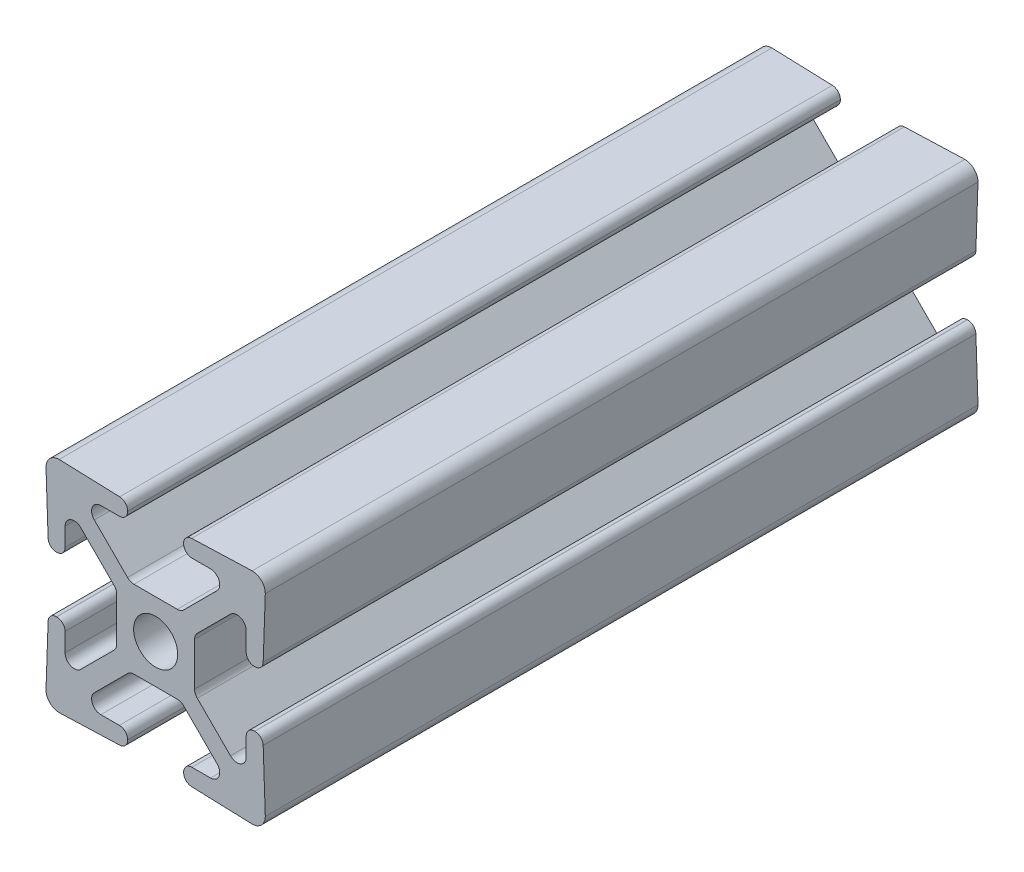
SolidWorks part; units mm, degrees
material "6061 Alloy"
ref_plane "Front Plane" through (0, 0, 0) normal (0, 0, 1) x (1, 0, 0)
ref_plane "Top Plane" through (0, 0, 0) normal (0, 1, 0) x (1, 0, 0)
ref_plane "Right Plane" through (0, 0, 0) normal (1, 0, 0) x (0, 0, -1)
sketch "Sketch1" plane through (0, 0, 0) normal (0, 0, 1) x (1, 0, 0)
  line L1 (3.2385, -11.4554) -> (3.2385, -11.4907)
  line L2 (-7.1065, 8.6691) -> (-3.2584, 4.821)
  line L3 (-3.2385, 11.4907) -> (-3.2385, 11.4554)
  line L6 (-4.2037, 10.4902) -> (-6.3521, 10.4902)
  line L7 (-11.176, 12.7) -> (-4.17, 12.4553)
  line L8 (11.4554, 3.2385) -> (11.4907, 3.2385)
  line L9 (11.4554, -3.2385) -> (11.4907, -3.2385)
  line L11 (-4.821, 3.2584) -> (-8.6691, 7.1065)
  line L12 (-10.4902, 6.3521) -> (-10.4902, 4.2037)
  line L13 (-12.7, 11.176) -> (-12.4553, 4.17)
  line L15 (-4.5085, -2.504) -> (-4.5085, 2.504)
  line L16 (6.3521, -10.4902) -> (4.2037, -10.4902)
  line L22 (-2.504, 4.5085) -> (2.504, 4.5085)
  line L23 (-3.2584, -4.821) -> (-7.1065, -8.6691)
  line L24 (-11.176, -12.7) -> (-4.17, -12.4553)
  line L25 (-12.7, -11.176) -> (-12.4553, -4.17)
  line L26 (-10.4902, -4.2037) -> (-10.4902, -6.3521)
  line L27 (-8.6691, -7.1065) -> (-4.821, -3.2584)
  line L36 (8.6691, -7.1065) -> (4.821, -3.2584)
  line L38 (10.4902, -4.2037) -> (10.4902, -6.3521)
  line L39 (12.7, -11.176) -> (12.4553, -4.17)
  line L42 (11.176, -12.7) -> (4.17, -12.4553)
  line L43 (3.2584, -4.821) -> (7.1065, -8.6691)
  line L47 (4.5085, -2.504) -> (4.5085, 2.504)
  line L48 (12.7, 11.176) -> (12.4553, 4.17)
  line L49 (10.4902, 6.3521) -> (10.4902, 4.2037)
  line L50 (4.821, 3.2584) -> (8.6691, 7.1065)
  line L52 (2.504, -4.5085) -> (-2.504, -4.5085)
  line L56 (11.176, 12.7) -> (4.17, 12.4553)
  line L57 (4.2037, 10.4902) -> (6.3521, 10.4902)
  line L59 (-6.3521, -10.4902) -> (-4.2037, -10.4902)
  line L60 (3.2385, 11.4907) -> (3.2385, 11.4554)
  line L61 (7.1065, 8.6691) -> (3.2584, 4.821)
  line L66 (-11.4554, -3.2385) -> (-11.4907, -3.2385)
  line L68 (-11.4554, 3.2385) -> (-11.4907, 3.2385)
  line L74 (-3.2385, -11.4554) -> (-3.2385, -11.4907)
  arc A1 (-3.2385, 11.4907) -> (-4.17, 12.4553) centre (-4.2037, 11.4907) ccw
  arc A4 (-4.2037, 10.4902) -> (-3.2385, 11.4554) centre (-4.2037, 11.4554) ccw
  arc A6 (-6.3521, 10.4902) -> (-7.1065, 8.6691) centre (-6.3521, 9.4234) ccw
  arc A8 (-12.4553, 4.17) -> (-11.4907, 3.2385) centre (-11.4907, 4.2037) ccw
  arc A9 (-11.176, 12.7) -> (-12.7, 11.176) centre (-11.176, 11.176) ccw
  arc A12 (-8.6691, 7.1065) -> (-10.4902, 6.3521) centre (-9.4234, 6.3521) ccw
  arc A13 (-11.4554, 3.2385) -> (-10.4902, 4.2037) centre (-11.4554, 4.2037) ccw
  arc A16 (-4.821, -3.2584) -> (-4.5085, -2.504) centre (-5.5753, -2.504) ccw
  arc A17 (-4.5085, 2.504) -> (-4.821, 3.2584) centre (-5.5753, 2.504) ccw
  arc A22 (3.2584, 4.821) -> (2.504, 4.5085) centre (2.504, 5.5753) cw
  arc A23 (10.4902, -6.3521) -> (8.6691, -7.1065) centre (9.4234, -6.3521) cw
  arc A24 (10.4902, -4.2037) -> (11.4554, -3.2385) centre (11.4554, -4.2037) cw
  arc A25 (11.4907, -3.2385) -> (12.4553, -4.17) centre (11.4907, -4.2037) cw
  arc A26 (12.7, -11.176) -> (11.176, -12.7) centre (11.176, -11.176) cw
  arc A28 (-2.504, -4.5085) -> (-3.2584, -4.821) centre (-2.504, -5.5753) ccw
  arc A29 (-4.17, -12.4553) -> (-3.2385, -11.4907) centre (-4.2037, -11.4907) ccw
  arc A30 (-3.2385, -11.4554) -> (-4.2037, -10.4902) centre (-4.2037, -11.4554) ccw
  arc A31 (-7.1065, -8.6691) -> (-6.3521, -10.4902) centre (-6.3521, -9.4234) ccw
  arc A32 (-12.7, -11.176) -> (-11.176, -12.7) centre (-11.176, -11.176) ccw
  arc A33 (-11.4907, -3.2385) -> (-12.4553, -4.17) centre (-11.4907, -4.2037) ccw
  arc A34 (-10.4902, -4.2037) -> (-11.4554, -3.2385) centre (-11.4554, -4.2037) ccw
  arc A35 (-10.4902, -6.3521) -> (-8.6691, -7.1065) centre (-9.4234, -6.3521) ccw
  arc A36 (7.1065, -8.6691) -> (6.3521, -10.4902) centre (6.3521, -9.4234) cw
  arc A37 (3.2385, -11.4554) -> (4.2037, -10.4902) centre (4.2037, -11.4554) cw
  arc A38 (-3.2584, 4.821) -> (-2.504, 4.5085) centre (-2.504, 5.5753) ccw
  arc A39 (4.17, -12.4553) -> (3.2385, -11.4907) centre (4.2037, -11.4907) cw
  arc A40 (2.504, -4.5085) -> (3.2584, -4.821) centre (2.504, -5.5753) cw
  circle A44 centre (0, 0) radius 2.5527
  arc A45 (4.5085, 2.504) -> (4.821, 3.2584) centre (5.5753, 2.504) cw
  arc A46 (4.821, -3.2584) -> (4.5085, -2.504) centre (5.5753, -2.504) cw
  arc A47 (11.4554, 3.2385) -> (10.4902, 4.2037) centre (11.4554, 4.2037) cw
  arc A48 (8.6691, 7.1065) -> (10.4902, 6.3521) centre (9.4234, 6.3521) cw
  arc A49 (11.176, 12.7) -> (12.7, 11.176) centre (11.176, 11.176) cw
  arc A53 (12.4553, 4.17) -> (11.4907, 3.2385) centre (11.4907, 4.2037) cw
  arc A54 (6.3521, 10.4902) -> (7.1065, 8.6691) centre (6.3521, 9.4234) cw
  arc A56 (4.2037, 10.4902) -> (3.2385, 11.4554) centre (4.2037, 11.4554) cw
  arc A58 (3.2385, 11.4907) -> (4.17, 12.4553) centre (4.2037, 11.4907) cw
  dimension "D5" = 5.1054
  dimension "D1" = 12.7
  dimension "D2" = 25.4
  dimension "D3" = 25.4
  dimension "D4" = 12.7
extrude "Extrude1" add sketch "Sketch1" along normal blind 82.55
sketch "Sketch2" plane through (0, 0, 0) normal (0, 0, -1) x (-1, 0, 0)
  point P0 (0, 0)
